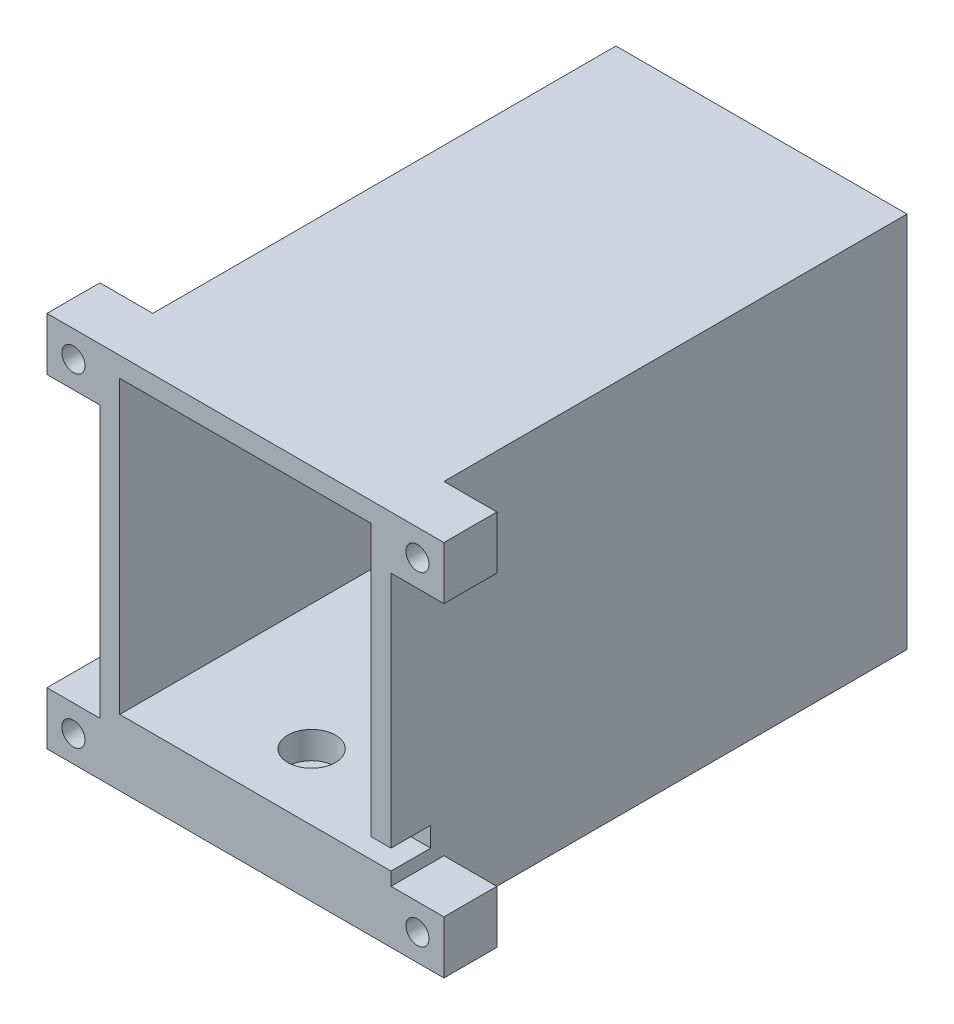
SolidWorks part; units mm, degrees
ref_plane "前基準面" through (0, 0, 0) normal (0, 0, 1) x (1, 0, 0)
ref_plane "上基準面" through (0, 0, 0) normal (0, 1, 0) x (1, 0, 0)
ref_plane "右基準面" through (0, 0, 0) normal (1, 0, 0) x (0, 0, -1)
sketch "草圖1" plane through (0, 0, 0) normal (0, 1, 0) x (1, 0, 0)
  line L1 (-22, 39) -> (22, 39)
  line L2 (-22, 39) -> (-22, -39)
  line L3 (-22, -39) -> (22, -39)
  line L4 (22, 39) -> (22, -39)
  line L5 (-22, 39) -> (22, -39) construction
  line L6 (-22, -39) -> (22, 39) construction
  point P0 (0, 0)
  dimension "D1" = 78
  dimension "D2" = 44
extrude "填料-伸長1" add sketch "草圖1" along normal blind 57
shell "薄殼1" thickness 3
sketch "草圖3" plane through (0, 10, 0) normal (0, 1, 0) x (1, 0, 0)
  line L0 (-22, -39) -> (22, -39) construction
  circle A0 centre (0, 25) radius 3.6
  circle A1 centre (0, -29) radius 3.6
  dimension "D1" = 7.2
  dimension "D2" = 54
  dimension "D3" = 10
extrude "除料-伸長1" cut sketch "草圖3" against normal blind 4.1
sketch "草圖4" plane through (0, 10, 0) normal (0, 1, 0) x (1, 0, 0)
  circle A0 centre (0, 25) radius 2.25
  circle A1 centre (0, -29) radius 2.25
  dimension "D1" = 4.5
extrude "除料-伸長2" cut sketch "草圖4" against normal up to next
sketch "草圖5" plane through (0, 0, 39) normal (0, 0, 1) x (1, 0, 0)
  line L0 (22, 57) -> (22, 0) construction
  line L1 (19, 10) -> (22, 10)
  line L2 (19, 10) -> (19, 13)
  line L3 (19, 13) -> (22, 13)
  line L4 (22, 10) -> (22, 13)
  dimension "D1" = 3
extrude "除料-伸長3" cut sketch "草圖5" against normal blind 6
sketch "草圖6" plane through (0, 0, 39) normal (0, 0, 1) x (1, 0, 0)
  line L0 (-22, 57) -> (-22, 0) construction
  line L1 (-30, 49) -> (-22, 49)
  line L2 (-30, 49) -> (-30, 57)
  line L3 (-30, 57) -> (-22, 57)
  line L4 (-22, 49) -> (-22, 57)
  line L5 (-30, 49) -> (-22, 57) construction
  line L6 (-30, 57) -> (-22, 49) construction
  line L7 (-30, 8) -> (-22, 8)
  line L8 (-30, 8) -> (-30, 0)
  line L9 (-30, 0) -> (-22, 0)
  line L10 (-22, 8) -> (-22, 0)
  line L11 (-30, 8) -> (-22, 0) construction
  line L12 (-30, 0) -> (-22, 8) construction
  line L13 (0, 0) -> (0, 16.0157) construction
  line L14 (30, 0) -> (22, 8) construction
  line L15 (30, 8) -> (22, 0) construction
  line L16 (30, 57) -> (22, 49) construction
  line L17 (30, 49) -> (22, 57) construction
  line L18 (22, 8) -> (22, 0)
  line L19 (30, 0) -> (22, 0)
  line L20 (30, 8) -> (30, 0)
  line L21 (30, 8) -> (22, 8)
  line L22 (22, 49) -> (22, 57)
  line L23 (30, 57) -> (22, 57)
  line L24 (30, 49) -> (30, 57)
  line L25 (30, 49) -> (22, 49)
  circle A0 centre (-26, 53) radius 1.75
  circle A1 centre (-26, 4) radius 1.75
  circle A2 centre (26, 4) radius 1.75
  circle A3 centre (26, 53) radius 1.75
  point P0 (-26, 53)
  point P6 (-26, 4)
  point P25 (26, 4)
  point P26 (26, 53)
  dimension "D3" = 3.5
  dimension "D1" = 8
  dimension "D2" = 8
extrude "填料-伸長2" add sketch "草圖6" against normal blind 8
sketch "草圖7" plane through (0, 0, 31) normal (0, 0, -1) x (-1, 0, 0)
  line L0 (0, 0) -> (0, 13.0726) construction
  line L1 (-22.8246, 53) -> (-24.4123, 55.75)
  line L2 (-24.4123, 55.75) -> (-27.5877, 55.75)
  line L3 (-27.5877, 55.75) -> (-29.1754, 53)
  line L4 (-29.1754, 53) -> (-27.5877, 50.25)
  line L5 (-27.5877, 50.25) -> (-24.4123, 50.25)
  line L6 (-24.4123, 50.25) -> (-22.8246, 53)
  line L7 (-22.8246, 4) -> (-24.4123, 6.75)
  line L8 (-24.4123, 6.75) -> (-27.5877, 6.75)
  line L9 (-27.5877, 6.75) -> (-29.1754, 4)
  line L10 (-29.1754, 4) -> (-27.5877, 1.25)
  line L11 (-27.5877, 1.25) -> (-24.4123, 1.25)
  line L12 (-24.4123, 1.25) -> (-22.8246, 4)
  line L13 (24.4123, 1.25) -> (22.8246, 4)
  line L14 (27.5877, 1.25) -> (24.4123, 1.25)
  line L15 (29.1754, 4) -> (27.5877, 1.25)
  line L16 (27.5877, 6.75) -> (29.1754, 4)
  line L17 (24.4123, 6.75) -> (27.5877, 6.75)
  line L18 (22.8246, 4) -> (24.4123, 6.75)
  line L19 (24.4123, 50.25) -> (22.8246, 53)
  line L20 (27.5877, 50.25) -> (24.4123, 50.25)
  line L21 (29.1754, 53) -> (27.5877, 50.25)
  line L22 (27.5877, 55.75) -> (29.1754, 53)
  line L23 (24.4123, 55.75) -> (27.5877, 55.75)
  line L24 (22.8246, 53) -> (24.4123, 55.75)
  circle A0 centre (-26, 53) radius 2.75 construction
  circle A1 centre (-26, 4) radius 2.75 construction
  circle A2 centre (26, 4) radius 2.75 construction
  circle A3 centre (26, 53) radius 2.75 construction
  dimension "D1" = 5.5
extrude "除料-伸長4" cut sketch "草圖7" against normal blind 2.6
sketch "草圖8" plane through (0, 0, -36) normal (0, 0, 1) x (1, 0, 0)
  circle A0 centre (0, 30) radius 5
  point P2 (0, 0)
  dimension "D1" = 10
  dimension "D2" = 30
extrude "除料-伸長5" cut sketch "草圖8" against normal up to next
